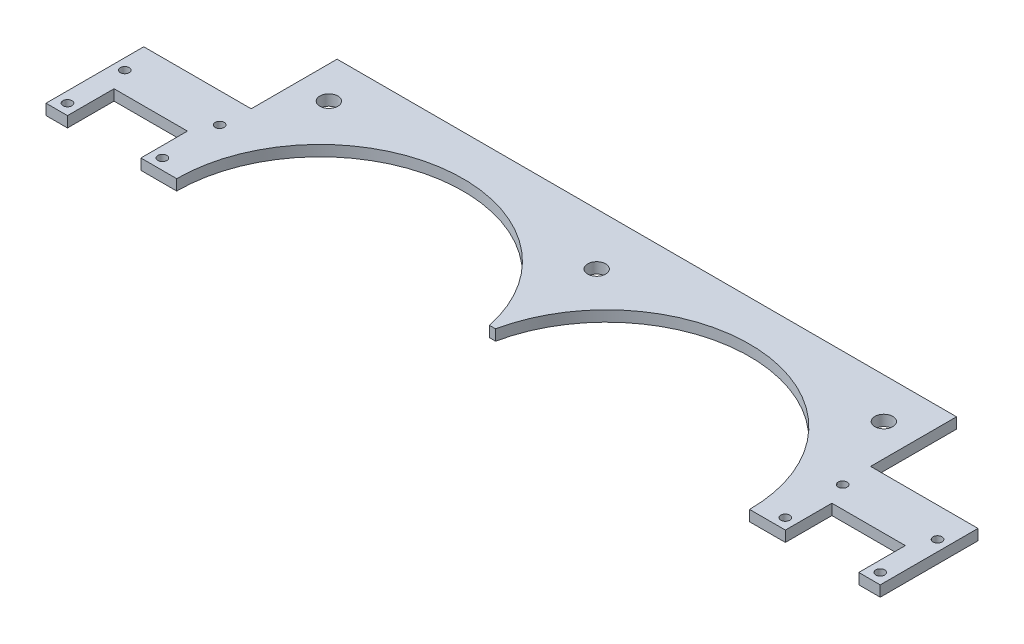
SolidWorks part; units mm, degrees
ref_plane "Face" through (0, 0, 0) normal (0, 0, 1) x (1, 0, 0)
ref_plane "Dessus" through (0, 0, 0) normal (0, 1, 0) x (1, 0, 0)
ref_plane "Droite" through (0, 0, 0) normal (1, 0, 0) x (0, 0, -1)
sketch "Esquisse1" plane through (0, 0, 0) normal (0, 1, 0) x (1, 0, 0)
  line L0 (-2.7503, 0) -> (-2.7503, 372.8366) construction
  line L1 (-2.7503, 0) -> (-2.7503, -232.7616) construction
  line L3 (110.7497, 11.7952) -> (84.2497, 11.7952) construction
  line L4 (-119.2503, 8.7952) -> (-113.2503, 8.7952)
  line L5 (-119.2503, 8.7952) -> (-119.2503, 36.099)
  line L6 (-119.2503, 36.099) -> (-89.2503, 36.099)
  line L7 (110.7497, 19.7952) -> (84.2497, 19.7952) construction
  line L9 (84.2497, 27.7952) -> (84.2497, 8.7952) construction
  line L10 (-89.2503, 60.099) -> (83.7497, 60.099)
  line L11 (110.7497, 27.7952) -> (84.2497, 27.7952) construction
  line L12 (110.7497, 8.7952) -> (110.7497, 27.7952) construction
  line L14 (113.7497, 8.7952) -> (81.7497, 8.7952) construction
  line L15 (87.2497, 8.7952) -> (77.2497, 8.7952)
  line L16 (87.2497, 21.7952) -> (87.2497, 8.7952)
  line L17 (107.7497, 21.7952) -> (87.2497, 21.7952)
  line L18 (-89.2503, 36.099) -> (-89.2503, 60.099)
  line L19 (107.7497, 8.7952) -> (107.7497, 21.7952)
  line L20 (-113.2503, 8.7952) -> (-113.2503, 21.7952)
  line L21 (-113.2503, 21.7952) -> (-92.7503, 21.7952)
  line L22 (-92.7503, 21.7952) -> (-92.7503, 8.7952)
  line L23 (-92.7503, 8.7952) -> (-82.7503, 8.7952)
  line L25 (83.7497, 36.099) -> (83.7497, 60.099)
  line L26 (113.7497, 36.099) -> (83.7497, 36.099)
  line L27 (113.7497, 8.7952) -> (113.7497, 36.099)
  line L28 (113.7497, 8.7952) -> (107.7497, 8.7952)
  line L30 (-3.601, 17.0006) -> (-1.8997, 17.0006)
  line L35 (-116.2503, 8.7952) -> (-116.2503, 27.7952) construction
  line L36 (-116.2503, 27.7952) -> (-89.7503, 27.7952) construction
  line L37 (-89.7503, 27.7952) -> (-89.7503, 8.7952) construction
  line L38 (-116.2503, 19.7952) -> (-89.7503, 19.7952) construction
  line L39 (-116.2503, 11.7952) -> (-89.7503, 11.7952) construction
  arc A0 (-82.7503, 8.7952) -> (-3.601, 17.0006) centre (-42.7503, 8.7952) cw
  circle A1 centre (110.7497, 11.7952) radius 1.25
  circle A2 centre (-2.2503, 45.599) radius 2.5
  circle A3 centre (84.2497, 27.7952) radius 1.25
  circle A4 centre (110.7497, 27.7952) radius 1.25
  circle A5 centre (-80.2503, 48.7952) radius 2.5
  circle A6 centre (74.7497, 48.7952) radius 2.5
  circle A7 centre (-116.2503, 27.7952) radius 1.25
  arc A8 (77.2497, 8.7952) -> (-1.8997, 17.0006) centre (37.2497, 8.7952) ccw
  circle A9 centre (-89.7503, 27.7952) radius 1.25
  circle A10 centre (-89.7503, 11.7952) radius 1.25
  circle A11 centre (84.2497, 11.7952) radius 1.25
  circle A14 centre (-116.2503, 11.7952) radius 1.25
  point P3 (-2.2503, 45.599)
  point P43 (-2.7503, 8.4913)
  point P58 (-2.7503, 60.099)
  point P59 (-2.7503, 8.4913)
  point P61 (-2.7503, 65.4701)
  dimension "D3" = 24
  dimension "D6" = 30
  dimension "D8" = 5
  dimension "D11" = 40
  dimension "D17" = 3
  dimension "D13" = 2.5
  dimension "D26" = 2.5
  dimension "D20" = 40
  dimension "D7" = 14.5
  dimension "D4" = 5
  dimension "D5" = 10
  dimension "D9" = 36
  dimension "D10" = 21
  dimension "D15" = 13
  dimension "D16" = 3
  dimension "D23" = 8
  dimension "D24" = 8
  dimension "D25" = 3
  dimension "D27" = 26.5
extrude "Extrusion1" add sketch "Esquisse1" along normal blind 3
